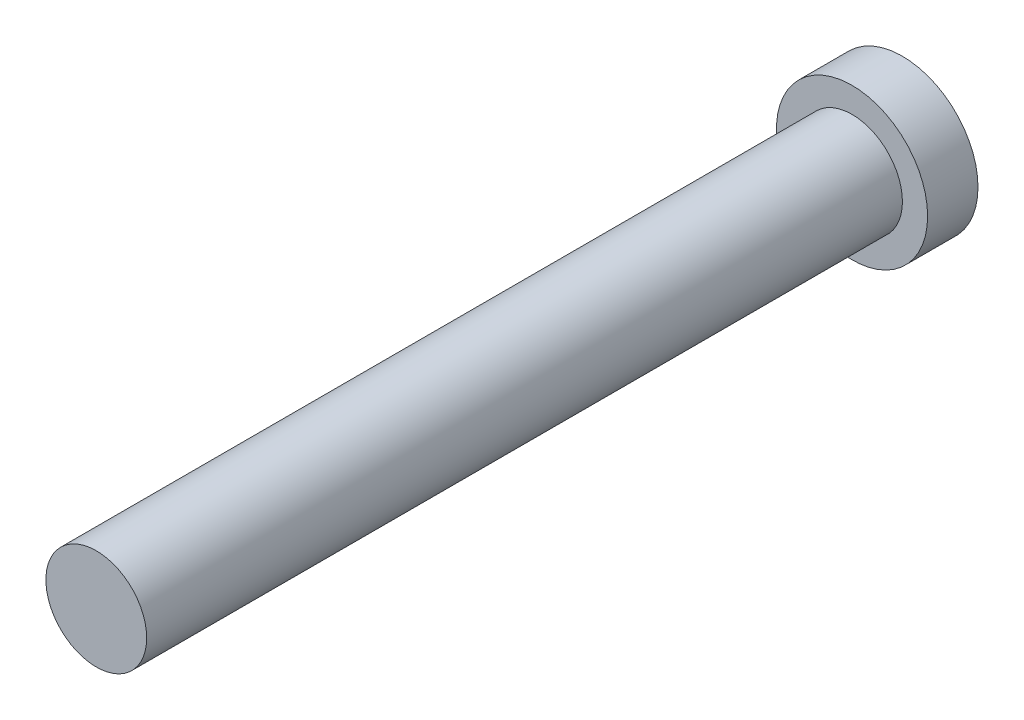
SolidWorks part; units mm, degrees
ref_plane "Front Plane" through (0, 0, 0) normal (0, 0, 1) x (1, 0, 0)
ref_plane "Top Plane" through (0, 0, 0) normal (0, 1, 0) x (1, 0, 0)
ref_plane "Right Plane" through (0, 0, 0) normal (1, 0, 0) x (0, 0, -1)
sketch "Sketch1" plane through (0, 0, 0) normal (0, 0, 1) x (1, 0, 0)
  circle A0 centre (0, 0) radius 3.81
  dimension "D1" = 7.62
extrude "Boss-Extrude1" add sketch "Sketch1" along normal blind 2.54
sketch "Sketch2" plane through (0, 0, 2.54) normal (0, 0, 1) x (1, 0, 0)
  circle A0 centre (0, 0) radius 2.54
  dimension "D1" = 5.08
extrude "Boss-Extrude2" add sketch "Sketch2" along normal blind 38.1
